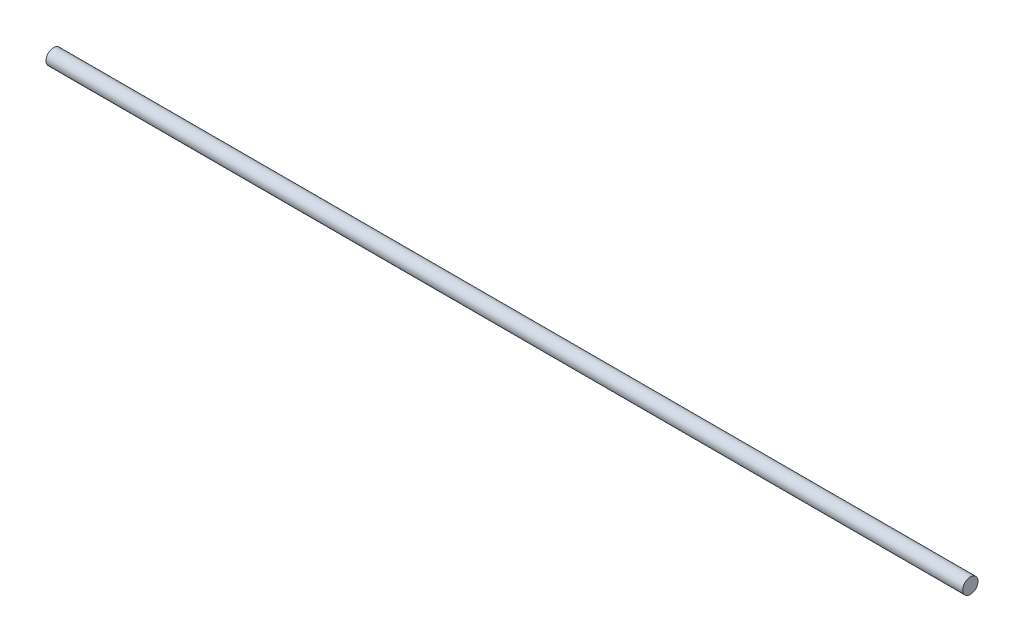
SolidWorks part; units mm, degrees
ref_plane "Front Plane" through (0, 0, 0) normal (0, 0, 1) x (1, 0, 0)
ref_plane "Top Plane" through (0, 0, 0) normal (0, 1, 0) x (1, 0, 0)
ref_plane "Right Plane" through (0, 0, 0) normal (1, 0, 0) x (0, 0, -1)
sketch "Sketch1" plane through (0, 0, 0) normal (1, 0, 0) x (0, 0, -1)
  circle A0 centre (0, 0) radius 6.35
  dimension "D1" = 12.7
extrude "Boss-Extrude2" add sketch "Sketch1" along normal blind 762
